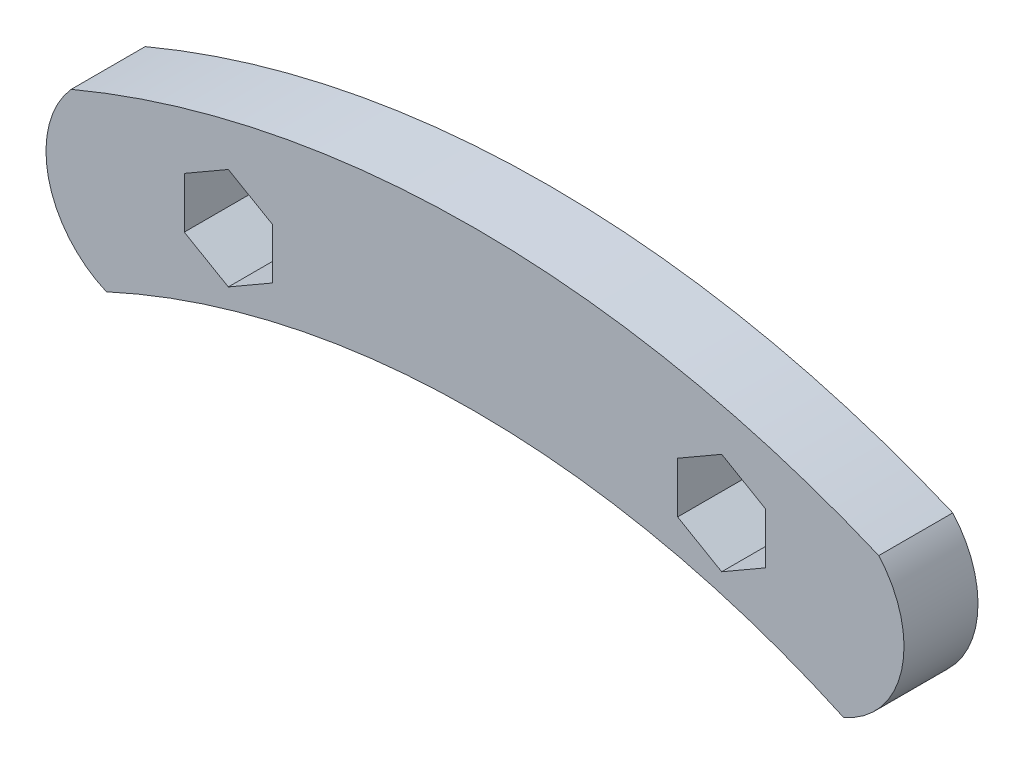
SolidWorks part; units mm, degrees
ref_plane "Front Plane" through (0, 0, 0) normal (0, 0, 1) x (1, 0, 0)
ref_plane "Top Plane" through (0, 0, 0) normal (0, 1, 0) x (1, 0, 0)
ref_plane "Right Plane" through (0, 0, 0) normal (1, 0, 0) x (0, 0, -1)
sketch "Sketch1" plane through (0, 0, 0) normal (0, 0, 1) x (1, 0, 0)
  line L1 (0, 96.3712) -> (0, -9.4867) construction
  line L2 (-17.78, 62.3738) -> (-14.605, 64.2069)
  line L3 (-14.605, 64.2069) -> (-14.605, 67.8731)
  line L4 (-14.605, 67.8731) -> (-17.78, 69.7062)
  line L5 (-17.78, 69.7062) -> (-20.955, 67.8731)
  line L6 (-20.955, 67.8731) -> (-20.955, 64.2069)
  line L7 (-20.955, 64.2069) -> (-17.78, 62.3738)
  line L8 (17.78, 62.3738) -> (20.955, 64.2069)
  line L9 (20.955, 64.2069) -> (20.955, 67.8731)
  line L10 (20.955, 67.8731) -> (17.78, 69.7062)
  line L11 (17.78, 69.7062) -> (14.605, 67.8731)
  line L12 (14.605, 67.8731) -> (14.605, 64.2069)
  line L13 (14.605, 64.2069) -> (17.78, 62.3738)
  arc A0 (29.1049, 69.0464) -> (-29.1049, 69.0464) centre (0, 0) ccw
  circle A1 centre (-17.78, 66.04) radius 1.5 construction
  circle A2 centre (17.78, 66.04) radius 1.5 construction
  arc A3 (26.5655, 57.676) -> (-26.5655, 57.676) centre (0, 0) ccw
  arc A4 (-29.1049, 69.0464) -> (-26.5655, 57.676) centre (-23.7487, 64.2739) ccw
  circle A5 centre (-17.78, 66.04) radius 3.175 construction
  arc A6 (29.1049, 69.0464) -> (26.5655, 57.676) centre (23.7487, 64.2739) cw
  circle A7 centre (17.78, 66.04) radius 3.175 construction
  dimension "D1" = 149.86
  dimension "D2" = 6.35
  dimension "D3" = 17.78
  dimension "D4" = 3
  dimension "D6" = 127
  dimension "D7" = 6.35
  dimension "D5" = 66.04
extrude "Boss-Extrude1" add sketch "Sketch1" along normal blind 5.334
sketch "Sketch2" plane through (0, 0, 0) normal (0, 0, 1) x (1, 0, 0)
  line L1 (0, 96.3712) -> (0, -9.4867) construction
  line L2 (-17.78, 62.3738) -> (-14.605, 64.2069)
  line L3 (-14.605, 64.2069) -> (-14.605, 67.8731)
  line L4 (-14.605, 67.8731) -> (-17.78, 69.7062)
  line L5 (-17.78, 69.7062) -> (-20.955, 67.8731)
  line L6 (-20.955, 67.8731) -> (-20.955, 64.2069)
  line L7 (-20.955, 64.2069) -> (-17.78, 62.3738)
  line L8 (17.78, 62.3738) -> (20.955, 64.2069)
  line L9 (20.955, 64.2069) -> (20.955, 67.8731)
  line L10 (20.955, 67.8731) -> (17.78, 69.7062)
  line L11 (17.78, 69.7062) -> (14.605, 67.8731)
  line L12 (14.605, 67.8731) -> (14.605, 64.2069)
  line L13 (14.605, 64.2069) -> (17.78, 62.3738)
  arc A0 (29.1049, 69.0464) -> (-29.1049, 69.0464) centre (0, 0) ccw
  circle A1 centre (-17.78, 66.04) radius 1.5 construction
  circle A2 centre (17.78, 66.04) radius 1.5 construction
  arc A3 (26.5655, 57.676) -> (-26.5655, 57.676) centre (0, 0) ccw
  arc A4 (-29.1049, 69.0464) -> (-26.5655, 57.676) centre (-23.7487, 64.2739) ccw
  circle A5 centre (-17.78, 66.04) radius 3.175 construction
  arc A6 (29.1049, 69.0464) -> (26.5655, 57.676) centre (23.7487, 64.2739) cw
  circle A7 centre (17.78, 66.04) radius 3.175 construction
  dimension "D1" = 149.86
  dimension "D2" = 6.35
  dimension "D3" = 17.78
  dimension "D4" = 3
  dimension "D6" = 127
  dimension "D7" = 6.35
  dimension "D5" = 66.04
